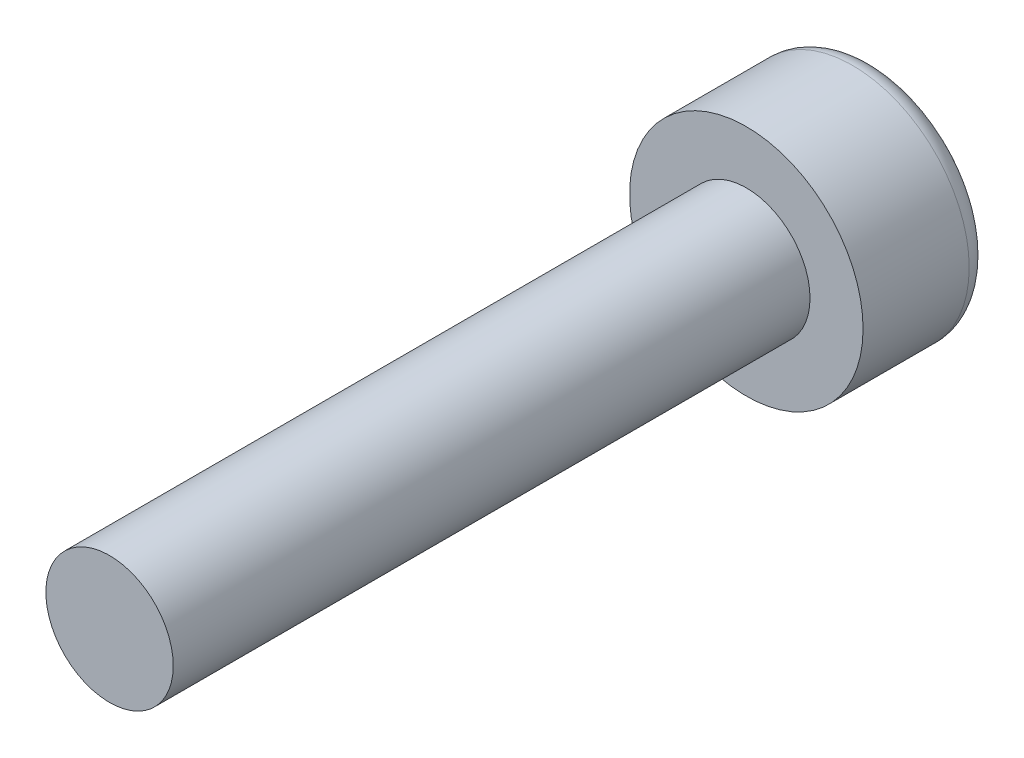
SolidWorks part; units mm, degrees
ref_plane "正面" through (0, 0, 0) normal (0, 0, 1) x (1, 0, 0)
ref_plane "平面" through (0, 0, 0) normal (0, 1, 0) x (1, 0, 0)
ref_plane "右側面" through (0, 0, 0) normal (1, 0, 0) x (0, 0, -1)
sketch "ｽｹｯﾁ2" plane through (0, 0, 0) normal (0, 0, 1) x (1, 0, 0)
  circle A0 centre (0, 0) radius 2.75
  dimension "D1" = 5.5
extrude "ﾎﾞｽ - 押し出し1" add sketch "ｽｹｯﾁ2" along normal blind 3
sketch "ｽｹｯﾁ3" plane through (0, 0, 3) normal (0, 0, 1) x (1, 0, 0)
  circle A0 centre (0, 0) radius 1.5
  dimension "D1" = 3
extrude "ﾎﾞｽ - 押し出し2" add sketch "ｽｹｯﾁ3" along normal blind 15
fillet "ﾌｨﾚｯﾄ1" radius 0.5 1 edges at (2.75, 0, 0)
